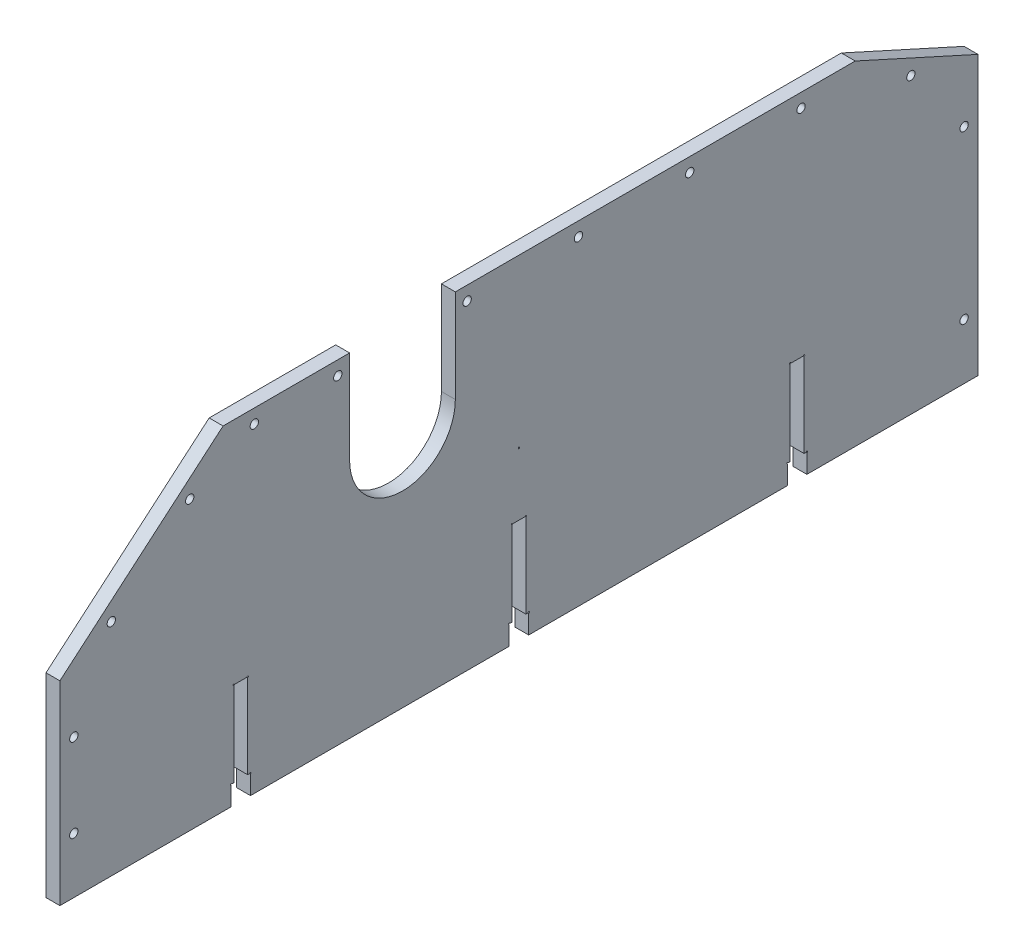
SolidWorks part; units mm, degrees
material "PMMA"
ref_plane "Front Plane" through (0, 0, 0) normal (0, 0, 1) x (1, 0, 0)
ref_plane "Top Plane" through (0, 0, 0) normal (0, 1, 0) x (1, 0, 0)
ref_plane "Right Plane" through (0, 0, 0) normal (1, 0, 0) x (0, 0, -1)
sketch "Schizzo1" plane through (0, 0, 0) normal (1, 0, 0) x (0, 0, -1)
  line L0 (165, 60) -> (-165, -60) construction
  line L1 (165, 60) -> (-106.354, 60)
  line L2 (-106.354, 60) -> (-165, 10)
  line L3 (-165, -60) -> (165, -60)
  line L4 (165, 60) -> (165, -60)
  line L5 (-165, 10) -> (-165, -60)
  point P0 (0, 0)
  dimension "D1" = 120
  dimension "D2" = 330
  dimension "D3" = 50
  dimension "D4" = 40.45
extrude "Estrusione-Estrusione1" add sketch "Schizzo1" along normal blind 5
sketch "Schizzo7" plane through (0, 0, 0) normal (1, 0, 0) x (0, 0, -1)
  line L0 (165, 40) -> (165, 60)
  line L1 (165, -60) -> (165, 60) construction
  line L2 (165, 60) -> (120.8693, 60)
  line L3 (165, 60) -> (-106.354, 60) construction
  line L4 (120.8693, 60) -> (165, 40)
  line L5 (-106.354, 60) -> (-106.354, -60) construction
  line L6 (-165, -60) -> (165, -60) construction
  line L7 (-165, -60) -> (165, -60) construction
  line L8 (-106.354, 60) -> (-165, 10) construction
  line L9 (-165, 10) -> (-165, -60) construction
  dimension "D1" = 100
  dimension "D2" = 24.38
  dimension "D3" = 49.55
  dimension "D4" = 65.62
  dimension "D5" = 155.62
extrude "Taglio-Estrusione5" cut sketch "Schizzo7" along direction (1, 0, 0) on the side of the normal through all
sketch "Schizzo2" plane through (5, 0, 0) normal (1, 0, 0) x (0, 0, -1)
  line L0 (0, -60) -> (0, 60) construction
  line L1 (-165, -60) -> (165, -60) construction
  line L3 (102.5, -60) -> (102.5, -22.5)
  line L4 (2.5, -60) -> (-2.5, -60)
  line L5 (2.5, -60) -> (2.5, -22.5)
  line L6 (2.5, -22.5) -> (-2.5, -22.5)
  line L7 (-2.5, -60) -> (-2.5, -22.5)
  line L8 (102.5, -22.5) -> (97.5, -22.5)
  line L9 (97.5, -60) -> (97.5, -22.5)
  line L10 (102.5, -60) -> (97.5, -60)
  line L11 (-97.5, -60) -> (-97.5, -22.5)
  line L12 (-97.5, -22.5) -> (-102.5, -22.5)
  line L13 (-102.5, -60) -> (-102.5, -22.5)
  line L14 (-97.5, -60) -> (-102.5, -60)
  line L15 (-100, -60) -> (-100, -22.5) construction
  line L16 (100, -60) -> (100, -22.5) construction
  point P10 (0, -22.5)
  dimension "D1" = 5
  dimension "D2" = 37.5
  dimension "D5" = 100
  dimension "D6" = 100
  dimension "D3" = 2
  dimension "D4" = 2
extrude "Taglio-Estrusione1" cut sketch "Schizzo2" along direction (1, 0, 0) on the side against the normal through all from surface at 0 starting at face at (5, 8.3333, -2.4192)
sketch "Schizzo3" plane through (0, 0, 0) normal (1, 0, 0) x (0, 0, -1)
  line L0 (-165, 10) -> (-165, -60) construction
  line L1 (-41.87, 26.5) -> (-41.87, 60) construction
  line L2 (-106.354, 60) -> (-165, 10) construction
  line L3 (-161.7561, 6.1951) -> (-103.11, 56.1951) construction
  line L4 (-41.87, 26.5) -> (-41.87, 60) construction
  line L5 (-60.87, 26.5) -> (-60.87, 60)
  line L6 (-22.87, 26.5) -> (-22.87, 60)
  line L7 (-165, -60) -> (-102.5, -60) construction
  line L8 (120.8693, 60) -> (-106.354, 60) construction
  line L9 (-160, 6.1951) -> (-160, -60) construction
  line L10 (-95.12, 55) -> (101.38, 55) construction
  line L11 (160, -60) -> (160, 42.266) construction
  line L12 (102.5, -60) -> (165, -60) construction
  line L13 (120.8693, 60) -> (165, 40) construction
  line L14 (165, -60) -> (165, 40) construction
  line L15 (108.7565, 60) -> (165, 34.5105) construction
  line L16 (120.8693, 60) -> (-106.354, 60) construction
  line L17 (147.4438, 59.9495) -> (138.4255, 40.0505) construction
  line L18 (165, -60) -> (165, 40) construction
  line L19 (165, -10) -> (125.4187, -10) construction
  line L20 (-165, 10) -> (-165, -60) construction
  line L22 (-165, 10) -> (-161.7561, 6.1951) construction
  line L23 (-106.354, 60) -> (-100.2094, 52.793) construction
  circle A0 centre (-65.12, 55) radius 1.5
  arc A1 (-60.87, 26.5) -> (-22.87, 26.5) centre (-41.87, 26.5) ccw
  arc A2 (-22.87, 60) -> (-60.87, 60) centre (-41.87, 60) ccw
  circle A3 centre (-18.62, 55) radius 1.5
  circle A4 centre (-95.12, 55) radius 1.5
  circle A5 centre (21.38, 55) radius 1.5
  circle A6 centre (61.38, 55) radius 1.5
  circle A7 centre (101.38, 55) radius 1.5
  circle A8 centre (-118.3295, 43.2195) radius 1.5
  circle A9 centre (-146.5366, 19.1708) radius 1.5
  circle A10 centre (-160, -10) radius 1.5
  circle A11 centre (-160, -40) radius 1.5
  circle A12 centre (160, -40) radius 1.5
  circle A14 centre (160, 20) radius 1.5
  circle A15 centre (140.8707, 45.4459) radius 1.5
  point P10 (-41.87, 43.25)
  point P63 (142.9347, 50)
  dimension "D2" = 23.25
  dimension "D3" = 19
  dimension "D4" = 3
  dimension "D8" = 5
  dimension "D12" = 5
  dimension "D17" = 5
  dimension "D21" = 40
  dimension "D22" = 5
  dimension "D11" = 3
  dimension "D1" = 123.13
  dimension "D5" = 2
  dimension "D6" = 5
  dimension "D9" = 20
  dimension "D10" = 20
  dimension "D13" = 30
  dimension "D15" = 20
  dimension "D16" = 5
  dimension "D18" = 30
  dimension "D20" = 33.5
  dimension "D23" = 40
  dimension "D14" = 20
  dimension "D19" = 40
  dimension "D7" = 4
extrude "Taglio-Estrusione2" cut sketch "Schizzo3" along direction (1, 0, 0) on the side of the normal through all
sketch "Schizzo8" plane through (5, 0, 0) normal (1, 0, 0) x (0, 0, -1)
  line L0 (-97.5, -60) -> (-2.5, -60) construction
  line L1 (-3.5, -60) -> (3.5, -60)
  line L2 (-3.5, -60) -> (-3.5, -53)
  line L3 (-3.5, -53) -> (3.5, -53)
  line L4 (3.5, -60) -> (3.5, -53)
  line L6 (0, -22.5) -> (0, -60) construction
  line L7 (-2.5, -22.5) -> (2.5, -22.5) construction
  line L8 (96.5, -60) -> (96.5, -53)
  line L9 (96.5, -53) -> (103.5, -53)
  line L10 (103.5, -60) -> (103.5, -53)
  line L11 (96.5, -60) -> (103.5, -60)
  line L12 (-103.5, -60) -> (-103.5, -53)
  line L13 (-103.5, -53) -> (-96.5, -53)
  line L14 (-96.5, -60) -> (-96.5, -53)
  line L15 (-103.5, -60) -> (-96.5, -60)
  point P11 (0, -53)
  dimension "D1" = 7
  dimension "D2" = 7
  dimension "D3" = 2
  dimension "D4" = 2
extrude "Taglio-Estrusione6" cut sketch "Schizzo8" against normal through all
sketch "Schizzo10" plane through (0, 0, 0) normal (1, 0, 0) x (0, 0, -1)
  line L0 (-96.5, -60) -> (-96.5, -53) construction
  line L1 (-2.5, -53) -> (-2.5, -22.5) construction
  line L2 (-2.5, -22.5) -> (2.5, -22.5) construction
  line L3 (96.5, -53) -> (96.5, -60) construction
  circle A0 centre (-102.5, -22.5) radius 0.25
  circle A1 centre (-97.5, -22.5) radius 0.25
  circle A2 centre (-103.5, -53) radius 0.25
  circle A3 centre (-96.5, -53) radius 0.25
  circle A4 centre (-2.5, -22.5) radius 0.25
  circle A5 centre (0, 0) radius 0.25
  circle A6 centre (2.5, -22.5) radius 0.25
  circle A7 centre (-3.5, -53) radius 0.25
  circle A8 centre (3.5, -53) radius 0.25
  circle A10 centre (97.5, -22.5) radius 0.25
  circle A11 centre (102.5, -22.5) radius 0.25
  circle A13 centre (96.5, -53) radius 0.25
  circle A14 centre (103.5, -53) radius 0.25
  dimension "D1" = 0.5
  dimension "D2" = 0.5
  dimension "D3" = 0.5
  dimension "D4" = 0.5
  dimension "D5" = 0.5
  dimension "D6" = 0.5
extrude "Taglio-Estrusione11" cut sketch "Schizzo10" along direction (1, 0, 0) on the side of the normal through all
equation "\"Thickness5\"= 5"
equation "\"D1@Estrusione-Estrusione1\"=\"Thickness5\""
equation "\"D1@Schizzo2\"=\"Thickness5\""
